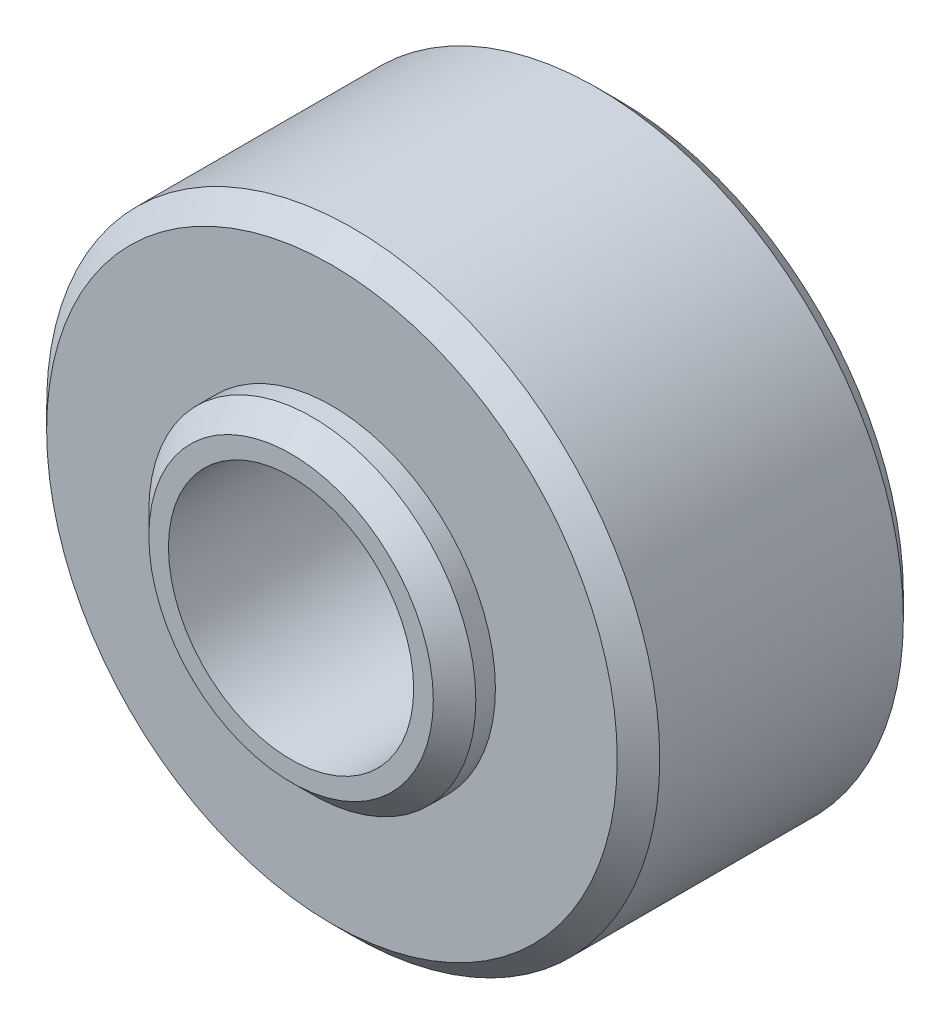
SolidWorks part; units mm, degrees
material "5052-O"
ref_plane "前基準面" through (0, 0, 0) normal (0, 0, 1) x (1, 0, 0)
ref_plane "上基準面" through (0, 0, 0) normal (0, 1, 0) x (1, 0, 0)
ref_plane "右基準面" through (0, 0, 0) normal (1, 0, 0) x (0, 0, -1)
sketch "Sketch1" plane through (0, 0, 0) normal (0, 0, 1) x (1, 0, 0)
  circle A0 centre (0, 0) radius 7.5
  dimension "D1" = 15
extrude "Boss-Extrude1" add sketch "Sketch1" along normal blind 7
sketch "Sketch2" plane through (0, 0, 7) normal (0, 0, 1) x (1, 0, 0)
  circle A0 centre (0, 0) radius 4
  dimension "D1" = 8
extrude "Boss-Extrude2" add sketch "Sketch2" along normal blind 1
sketch "Sketch3" plane through (0, 0, 8) normal (0, 0, 1) x (1, 0, 0)
  circle A0 centre (0, 0) radius 3
  dimension "D1" = 6
extrude "Cut-Extrude1" cut sketch "Sketch3" against normal through all
chamfer "Chamfer1" distance 0.52 angle 45 4 edges at (7.5, 0, 7) (7.5, 0, 0) (4, 0, 8) (3, 0, 0)
